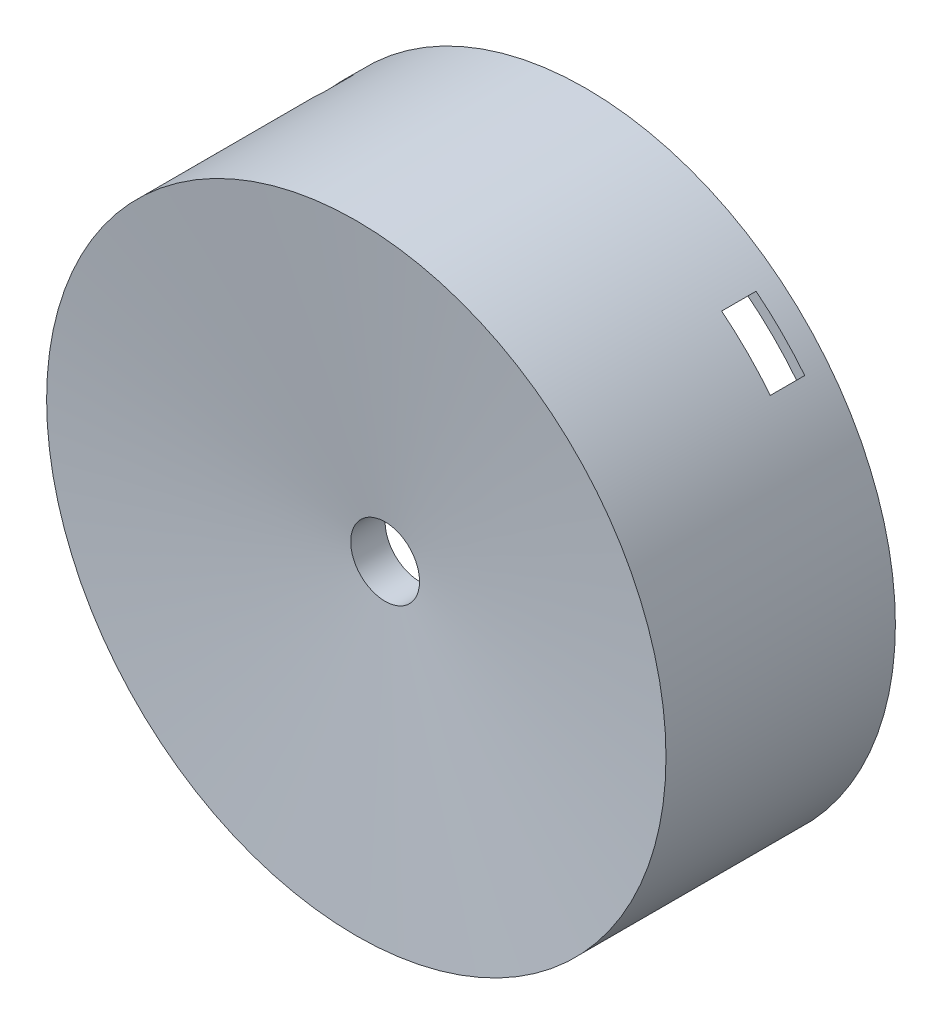
SolidWorks part; units mm, degrees
ref_plane "Plan de face" through (0, 0, 0) normal (0, 0, 1) x (1, 0, 0)
ref_plane "Plan de dessus" through (0, 0, 0) normal (0, 1, 0) x (1, 0, 0)
ref_plane "Plan de droite" through (0, 0, 0) normal (1, 0, 0) x (0, 0, -1)
sketch "Esquisse3" plane through (0, 0, 0) normal (0, 1, 0) x (1, 0, 0)
  line L0 (-27, 18.4138) -> (-27, 38.4138)
  line L1 (-27, 38.4138) -> (-26, 38.4138)
  line L2 (-26, 38.4138) -> (-26, 33.4138)
  line L3 (-26, 33.4138) -> (-25.5, 33.4138)
  line L4 (-3, 23.9269) -> (-3, 20.9269)
  line L5 (0, 0) -> (0, 34.9902) construction
  line L6 (-27, 18.4138) -> (-3, 20.9269)
  line L7 (-25.5, 33.4138) -> (-25.5, 19.5764)
  line L8 (-25.5, 19.5764) -> (-3.5, 21.88)
  line L9 (-3.5, 21.88) -> (-3.5, 23.9269)
  line L10 (-3.5, 23.9269) -> (-3, 23.9269)
  dimension "D1" = 26
  dimension "D2" = 1
  dimension "D3" = 5
  dimension "D4" = 0
  dimension "D5" = 20
  dimension "D7" = 3
  dimension "D8" = 0.5
  dimension "D9" = 0.5
  dimension "D10" = 1
  dimension "D11" = 3
revolve "Révolution1" add sketch "Esquisse3" angle 360 about L5
sketch "Esquisse7" plane through (0, 0, -33.4138) normal (0, 0, -1) x (-1, 0, 0)
  line L0 (25.923, -2) -> (22.923, -1)
  line L1 (22.923, -1) -> (22.923, 1)
  line L2 (22.923, 1) -> (25.923, 2)
  line L3 (25.923, 2) -> (25.923, -2)
  line L4 (-24.9199, 2) -> (-21.923, 0.9907)
  line L5 (-24.9322, -2) -> (-24.9199, 2)
  line L6 (-21.9291, -1.0092) -> (-24.9322, -2)
  line L7 (-21.923, 0.9907) -> (-21.9291, -1.0092)
  line L8 (22.5812, 10.7279) -> (19.483, 10.0945)
  line L9 (19.483, 10.0945) -> (18.4834, 11.8268)
  line L10 (18.4834, 11.8268) -> (20.5819, 14.1924)
  line L11 (20.5819, 14.1924) -> (22.5812, 10.7279)
  line L12 (-20.5812, 14.192) -> (-18.49, 11.8199)
  line L13 (-18.49, 11.8199) -> (-19.495, 10.0908)
  line L14 (-19.495, 10.0908) -> (-22.5912, 10.7337)
  line L15 (-22.5912, 10.7337) -> (-20.5812, 14.192)
  line L16 (20.5812, -14.192) -> (18.4973, -11.8135)
  line L17 (22.6018, -10.7398) -> (20.5812, -14.192)
  line L18 (19.5075, -10.0875) -> (22.6018, -10.7398)
  line L19 (18.4973, -11.8135) -> (19.5075, -10.0875)
  line L20 (-22.5812, -10.7279) -> (-19.4811, -10.1041)
  line L21 (-20.5927, -14.1986) -> (-22.5812, -10.7279)
  line L22 (-18.4868, -11.8394) -> (-20.5927, -14.1986)
  line L23 (-19.4811, -10.1041) -> (-18.4868, -11.8394)
  line L24 (20.293, -10.7099) -> (23.3872, -11.3623)
  circle A0 centre (0, 0) radius 26 construction
  point P4 (25.923, 0)
  point P7 (22.923, 0)
  point P9 (19.9899, 0)
  point P10 (19.9899, 0)
  point P18 (0.4985, -0.0392)
  point P22 (0, 0)
  point P25 (0.4921, -1.8743)
  point P28 (0, 0)
  point P33 (0.7688, 1.7547)
  point P37 (0.5092, 0.0916)
  point P41 (0.489, -0.1703)
  circle M10 centre (0, 0) radius 25.5
  dimension "D1" = 2
  dimension "D2" = 4
  dimension "D3" = 0
  dimension "D4" = 0
  dimension "D5" = 3
  dimension "D6" = 2
  dimension "D9" = 2
  dimension "D10" = 2
  dimension "D7" = 2
  dimension "D8" = 2
extrude "Boss.-Extru.4" add sketch "Esquisse7" against normal up to next contours L2 L1 L0 M10 | L14 L13 L12 M10 | L18 L17 L16 L19 | L9 L10 L11 L8 | L20 L23 L22 L21 | L4 L7 L6 L5
sketch "Esquisse8" plane through (0, 0, -33.4138) normal (0, 0, -1) x (-1, 0, 0)
  line L1 (10.2646, 12.386) -> (23.6744, 25.7957)
  line L2 (10.2646, 12.386) -> (12.386, 10.2646)
  line L3 (12.386, 10.2646) -> (25.7957, 23.6744)
  line L4 (23.6744, 25.7957) -> (25.7957, 23.6744)
  dimension "D1" = 1.5
  dimension "D2" = 1.5
extrude "Enlèv. mat.-Extru.2" cut sketch "Esquisse8" along normal blind 3
sketch "Esquisse9" plane through (0, 0, -33.4138) normal (0, 0, -1) x (-1, 0, 0)
  line L1 (-12.0208, 16.2635) -> (-19.0919, 23.3345)
  line L2 (-12.0208, 16.2635) -> (-16.2635, 12.0208)
  line L3 (-16.2635, 12.0208) -> (-23.3345, 19.0919)
  line L4 (-19.0919, 23.3345) -> (-23.3345, 19.0919)
  dimension "D1" = 3
  dimension "D2" = 3
  dimension "D3" = 10
  dimension "D4" = 20
extrude "Enlèv. mat.-Extru.3" cut sketch "Esquisse9" along normal blind 3
